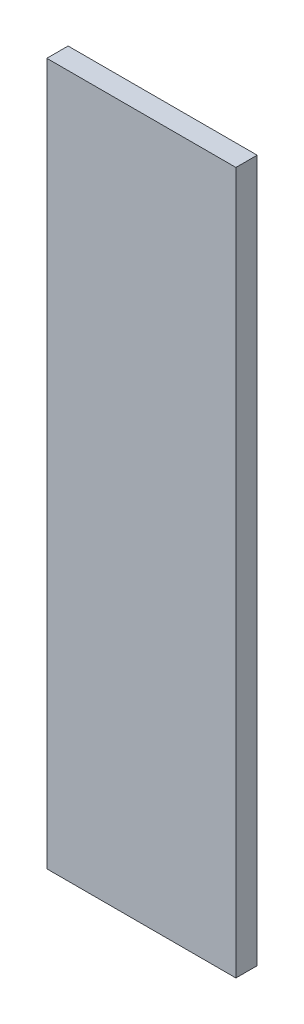
SolidWorks part; units mm, degrees
ref_plane "Front Plane" through (0, 0, 0) normal (0, 0, 1) x (1, 0, 0)
ref_plane "Top Plane" through (0, 0, 0) normal (0, 1, 0) x (1, 0, 0)
ref_plane "Right Plane" through (0, 0, 0) normal (1, 0, 0) x (0, 0, -1)
sketch "Sketch1" plane through (0, 0, 0) normal (0, 0, 1) x (1, 0, 0)
  line L1 (80, -297) -> (-80, -297)
  line L2 (80, -297) -> (80, 297)
  line L3 (80, 297) -> (-80, 297)
  line L4 (-80, -297) -> (-80, 297)
  line L5 (80, -297) -> (-80, 297) construction
  line L6 (80, 297) -> (-80, -297) construction
  point P0 (0, 0)
  dimension "D1" = 594
  dimension "D2" = 160
extrude "Boss-Extrude1" add sketch "Sketch1" along normal blind 18
equation "\"H_DSP\"=18"
equation "\"D1@Boss-Extrude1\"=\"H_DSP\""
